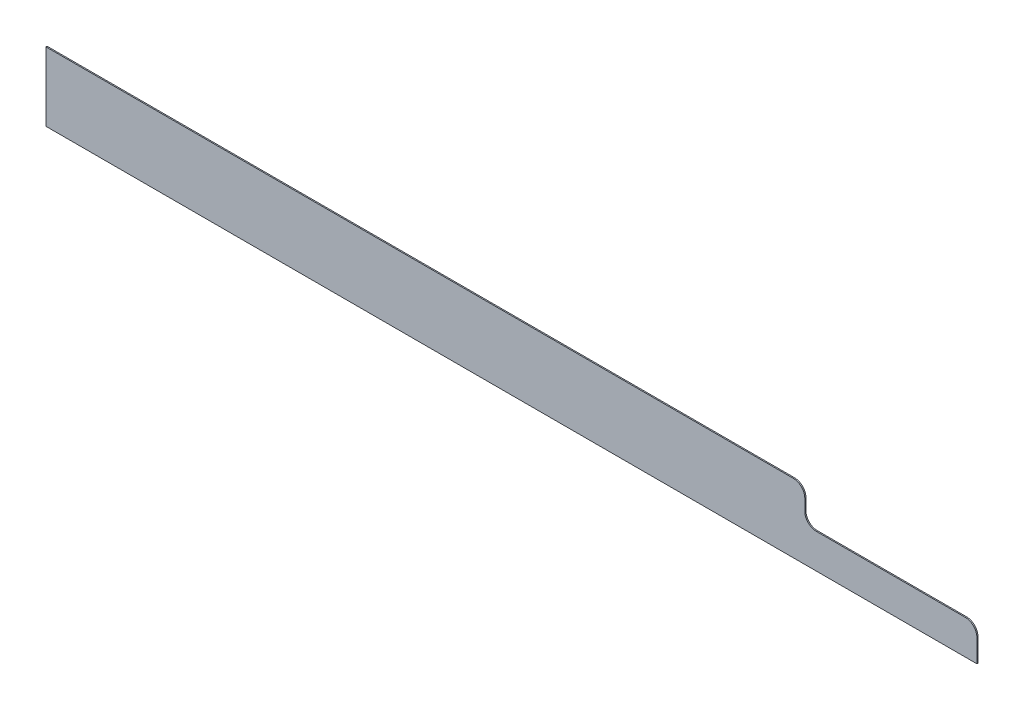
SolidWorks part; units mm, degrees
material "Acier non allié"
ref_plane "Plan de face" through (0, 0, 0) normal (0, 0, 1) x (1, 0, 0)
ref_plane "Plan de dessus" through (0, 0, 0) normal (0, 1, 0) x (1, 0, 0)
ref_plane "Plan de droite" through (0, 0, 0) normal (1, 0, 0) x (0, 0, -1)
sketch "Esquisse1" plane through (0, 0, 0) normal (0, 0, 1) x (1, 0, 0)
  line L0 (653.5, 120) -> (669.5, 120)
  line L1 (-653.5, 0) -> (653.5, 0)
  line L2 (-653.5, 0) -> (-653.5, 120)
  line L3 (-653.5, 120) -> (653.5, 120)
  line L4 (669.5, 60) -> (969.5, 60)
  line L5 (969.5, 60) -> (969.5, 0)
  line L6 (969.5, 0) -> (653.5, 0)
  line L7 (669.5, 120) -> (669.5, 60)
  dimension "D1" = 1307
  dimension "D2" = 120
  dimension "D3" = 60
  dimension "D4" = 16
  dimension "D5" = 300
extrude "Boss.-Extru.1" add sketch "Esquisse1" along normal blind 2
fillet "Congé1" radius 20 3 edges at (969.5, 60, 1) (669.5, 120, 1) (669.5, 60, 1)
